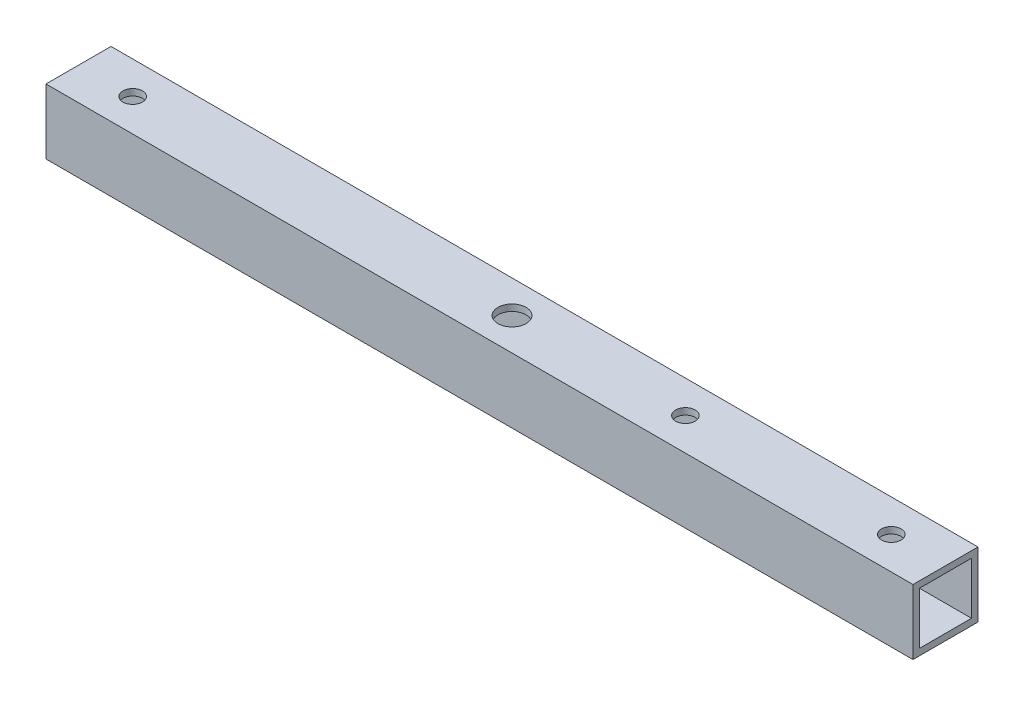
SolidWorks part; units mm, degrees
ref_plane "Front Plane" through (0, 0, 0) normal (0, 0, 1) x (1, 0, 0)
ref_plane "Top Plane" through (0, 0, 0) normal (0, 1, 0) x (1, 0, 0)
ref_plane "Right Plane" through (0, 0, 0) normal (1, 0, 0) x (0, 0, -1)
sketch "Sketch1" plane through (0, 0, 0) normal (1, 0, 0) x (0, 0, -1)
  line L0 (-6, 6) -> (6, 6)
  line L1 (-7.5, 7.5) -> (7.5, 7.5)
  line L2 (-7.5, 7.5) -> (-7.5, -7.5)
  line L3 (-7.5, -7.5) -> (7.5, -7.5)
  line L4 (7.5, 7.5) -> (7.5, -7.5)
  line L5 (-7.5, 7.5) -> (7.5, -7.5) construction
  line L6 (-7.5, -7.5) -> (7.5, 7.5) construction
  line L7 (6, 6) -> (6, -6)
  line L8 (-6, -6) -> (6, -6)
  line L9 (-6, 6) -> (-6, -6)
  point P0 (0, 0)
  dimension "D1" = 15
  dimension "D2" = 15
  dimension "D3" = 1.5
extrude "Boss-Extrude1" add sketch "Sketch1" along normal blind 200
sketch "Sketch2" plane through (0, 7.5, 0) normal (0, 1, 0) x (1, 0, 0)
  line L0 (0, 0) -> (200, 0) construction
  line L1 (200, 7.5) -> (200, -7.5) construction
  circle A0 centre (100, 0) radius 3.25
  circle A1 centre (140, 0) radius 2.25
  dimension "D1" = 6.5
  dimension "D2" = 4.5
  dimension "D3" = 40
extrude "Cut-Extrude1" cut sketch "Sketch2" against normal through all
sketch "Sketch3" plane through (0, 7.5, 0) normal (0, 1, 0) x (1, 0, 0)
  line L0 (100, 7.5) -> (100, -7.5) construction
  line L1 (200, 7.5) -> (0, 7.5) construction
  line L2 (200, -7.5) -> (0, -7.5) construction
  line L3 (0, 0) -> (12.5, 0) construction
  circle A0 centre (12.5, 0) radius 2.25
  circle A1 centre (187.5, 0) radius 2.25
  dimension "D1" = 4.5
  dimension "D2" = 12.5
extrude "Cut-Extrude2" cut sketch "Sketch3" against normal through all
